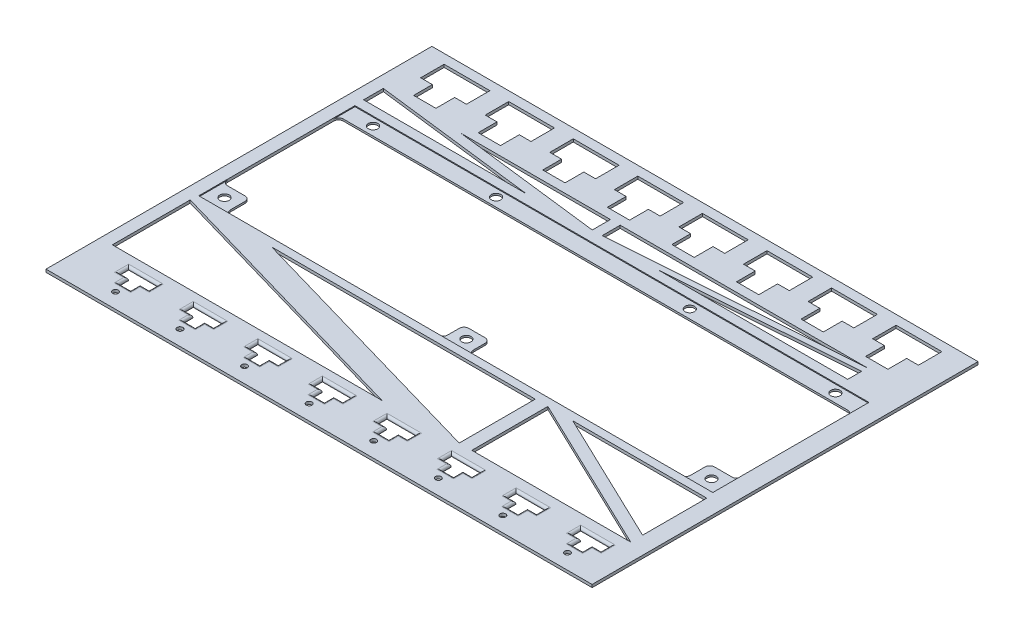
SolidWorks part; units mm, degrees
ref_plane "Front Plane" through (0, 0, 0) normal (0, 0, 1) x (1, 0, 0)
ref_plane "Top Plane" through (0, 0, 0) normal (0, 1, 0) x (1, 0, 0)
ref_plane "Right Plane" through (0, 0, 0) normal (1, 0, 0) x (0, 0, -1)
sketch "Sketch1" plane through (0, 0, 0) normal (0, 1, 0) x (1, 0, 0)
  line L1 (-15, 0) -> (245, 0)
  line L2 (-15, 0) -> (-15, 186.9)
  line L3 (-15, 186.9) -> (245, 186.9)
  line L4 (245, 0) -> (245, 186.9)
  dimension "D1" = 186.9
  dimension "D2" = 260
extrude "Boss-Extrude1" add sketch "Sketch1" along normal blind 1.2
sketch "Sketch2" plane through (0, 0, 0) normal (0, 1, 0) x (1, 0, 0)
  line L0 (245, 186.9) -> (-15, 186.9) construction
  line L1 (17.91, 148.65) -> (236.81, 148.65)
  line L2 (17.91, 148.65) -> (17.91, 82.15)
  line L3 (17.91, 82.15) -> (236.81, 82.15)
  line L4 (236.81, 148.65) -> (236.81, 82.15)
  line L5 (-15, 186.9) -> (-15, 0) construction
  dimension "D1" = 38.25
  dimension "D2" = 32.91
  dimension "D3" = 66.5
  dimension "D4" = 218.9
extrude "Cut-Extrude1" cut sketch "Sketch2" along normal blind 9
sketch "Sketch3" plane through (0, 1.2, 0) normal (0, 1, 0) x (1, 0, 0)
  line L0 (236.81, 148.65) -> (17.91, 148.65) construction
  line L1 (17.91, 148.65) -> (17.91, 82.15) construction
  line L2 (17.91, 82.15) -> (236.81, 82.15) construction
  circle A0 centre (28.91, 145.35) radius 2
  circle A1 centre (81.31, 145.35) radius 2
  circle A2 centre (163.81, 145.35) radius 2
  circle A3 centre (225.81, 145.35) radius 2
  circle A4 centre (23.66, 87.35) radius 2
  circle A5 centre (127.36, 86.65) radius 2
  circle A6 centre (231.06, 87.35) radius 2
  dimension "D3" = 4
  dimension "D4" = 3.3
  dimension "D6" = 3.3
  dimension "D8" = 3.3
  dimension "D10" = 5.2
  dimension "D12" = 4.5
  dimension "D14" = 5.2
  dimension "D1" = 3.3
  dimension "D2" = 11
  dimension "D5" = 52.4
  dimension "D7" = 82.5
  dimension "D9" = 62
  dimension "D11" = 5.75
  dimension "D13" = 103.7
  dimension "D15" = 103.7
sketch "Sketch4" plane through (0, 0, 0) normal (0, 1, 0) x (1, 0, 0)
  line L0 (236.81, 82.15) -> (236.81, 148.65) construction
  line L1 (17.91, 148.65) -> (236.81, 148.65)
  line L2 (17.91, 148.65) -> (17.91, 141.65)
  line L3 (17.91, 141.65) -> (236.81, 141.65)
  line L4 (236.81, 148.65) -> (236.81, 141.65)
  line L5 (17.91, 82.15) -> (236.81, 82.15) construction
  line L6 (236.81, 82.15) -> (225.31, 82.15)
  line L7 (236.81, 82.15) -> (236.81, 92.35)
  line L8 (236.81, 92.35) -> (225.31, 92.35)
  line L9 (225.31, 82.15) -> (225.31, 92.35)
  line L10 (121.86, 82.15) -> (132.86, 82.15)
  line L11 (121.86, 82.15) -> (121.86, 91.15)
  line L12 (121.86, 91.15) -> (132.86, 91.15)
  line L13 (132.86, 82.15) -> (132.86, 91.15)
  line L15 (17.91, 82.15) -> (29.41, 82.15)
  line L16 (17.91, 82.15) -> (17.91, 92.35)
  line L17 (17.91, 92.35) -> (29.41, 92.35)
  line L18 (29.41, 82.15) -> (29.41, 92.35)
  dimension "D1" = 7
  dimension "D2" = 5
  dimension "D3" = 5.75
  dimension "D4" = 4.5
  dimension "D5" = 5.5
  dimension "D6" = 5.5
  dimension "D7" = 5.75
  dimension "D8" = 5
extrude "Boss-Extrude2" add sketch "Sketch4" along normal blind 0.8
extrude "Cut-Extrude2" cut sketch "Sketch3" against normal blind 10
fillet "Fillet1" radius 2 12 edges at (17.91, 0.4, -92.35) (29.41, 0.4, -82.15) (29.41, 0.4, -92.35) (17.91, 0.4, -141.65) (236.81, 0.4, -141.65) (236.81, 0.4, -92.35) (225.31, 0.4, -82.15) (225.31, 0.4, -92.35) (121.86, 0.4, -82.15) (132.86, 0.4, -82.15) (132.86, 0.4, -91.15) (121.86, 0.4, -91.15)
sketch "Sketch10" plane through (0, 1.2, 0) normal (0, 1, 0) x (1, 0, 0)
  line L0 (245, 186.9) -> (-15, 186.9) construction
  line L1 (21.63, 182.9) -> (41.13, 182.9)
  line L2 (21.63, 182.9) -> (21.63, 172.9)
  line L3 (21.63, 172.9) -> (41.13, 172.9)
  line L4 (41.13, 182.9) -> (41.13, 172.9)
  line L5 (17.91, 148.65) -> (17.91, 82.15) construction
  dimension "D1" = 4
  dimension "D2" = 19.5
  dimension "D3" = 3.72
  dimension "D4" = 10
extrude "Cut-Extrude4" cut sketch "Sketch10" against normal up to next (1.2 mm away)
sketch "Sketch11" plane through (0, 1.2, 0) normal (0, 1, 0) x (1, 0, 0)
  line L0 (21.63, 172.9) -> (41.13, 172.9) construction
  line L1 (26.63, 172.9) -> (36.13, 172.9)
  line L2 (26.63, 172.9) -> (26.63, 164.9)
  line L3 (26.63, 164.9) -> (36.13, 164.9)
  line L4 (36.13, 172.9) -> (36.13, 164.9)
  line L5 (41.13, 172.9) -> (41.13, 182.9) construction
  line L6 (21.63, 182.9) -> (21.63, 172.9) construction
  dimension "D1" = 8
  dimension "D2" = 5
  dimension "D3" = 5
extrude "Cut-Extrude5" cut sketch "Sketch11" against normal blind 7
pattern_linear "LPattern1" count 8 spacing 27.5 along (1, 0, 0) of "Cut-Extrude4", "Cut-Extrude5"
sketch "Sketch14" plane through (0, 1.2, 0) normal (0, 1, 0) x (1, 0, 0)
  line L0 (-15, 186.9) -> (-15, 0) construction
  line L1 (29.19, 37) -> (33.04, 37)
  line L2 (29.19, 37) -> (29.19, 41)
  line L3 (29.19, 41) -> (41.89, 41)
  line L4 (41.89, 37) -> (41.89, 41)
  line L5 (38.04, 37) -> (41.89, 37)
  line L7 (-15, 0) -> (245, 0) construction
  line L8 (33.04, 37) -> (33.04, 33)
  line L9 (33.04, 33) -> (38.04, 33)
  line L10 (38.04, 37) -> (38.04, 33)
  circle A0 centre (35.54, 29) radius 1.2
  dimension "D8" = 2.4
  dimension "D9" = 4
  dimension "D10" = 2.5
  dimension "D1" = 44.19
  dimension "D2" = 12.7
  dimension "D3" = 37
  dimension "D4" = 4
  dimension "D5" = 3.85
  dimension "D6" = 3.85
  dimension "D7" = 4
extrude "Cut-Extrude8" cut sketch "Sketch14" against normal up to next (1.2 mm away)
fillet "Fillet2" radius 1 8 edges at (29.19, 1.2, -39) (33.04, 1.2, -35) (31.115, 1.2, -37) (39.965, 1.2, -37) (41.89, 1.2, -39) (35.54, 1.2, -41) (38.04, 1.2, -35) (35.54, 1.2, -33)
pattern_linear "LPattern4" count 8 spacing 27.5 along (1, 0, 0) of "Cut-Extrude8", "Fillet2"
sketch "Sketch15" plane through (0, 1.2, 0) normal (0, 1, 0) x (1, 0, 0)
  line L0 (-15, 0) -> (245, 0) construction
  line L1 (-15, 186.9) -> (12.421, 186.9)
  line L2 (-15, 186.9) -> (-15, 0)
  line L3 (-15, 0) -> (12.421, 0)
  line L4 (12.421, 186.9) -> (12.421, 22.5534)
  line L5 (17.5952, 161.0383) -> (17.5952, 152.6302)
  line L6 (17.5952, 152.6302) -> (86.9298, 152.6302)
  line L7 (86.9298, 152.6302) -> (17.5952, 161.0383)
  line L8 (50.5809, 161.0383) -> (114.3102, 153.3099)
  line L9 (114.3102, 153.3099) -> (114.3102, 161.0383)
  line L10 (114.3102, 161.0383) -> (50.5809, 161.0383)
  line L11 (118.4926, 161.0383) -> (118.4926, 153.3099)
  line L12 (118.4926, 153.3099) -> (223.7881, 161.0383)
  line L13 (223.7881, 161.0383) -> (118.4926, 161.0383)
  line L14 (143.1995, 152.6302) -> (223.7881, 158.5451)
  line L15 (223.7881, 158.5451) -> (223.7881, 152.6302)
  line L16 (223.7881, 152.6302) -> (143.1995, 152.6302)
  line L17 (17.5952, 78.7908) -> (17.5952, 45.6512)
  line L18 (17.5952, 45.6512) -> (132.457, 45.6512)
  line L19 (132.457, 45.6512) -> (17.5952, 78.7908)
  line L20 (52.2625, 78.7908) -> (164.5575, 46.3917)
  line L21 (164.5575, 46.3917) -> (164.5575, 78.7908)
  line L22 (164.5575, 78.7908) -> (52.2625, 78.7908)
  line L23 (169.9222, 78.7908) -> (169.9222, 46.3917)
  line L24 (169.9222, 46.3917) -> (237.5932, 46.3917)
  line L25 (237.5932, 46.3917) -> (169.9222, 78.7908)
  line L26 (180.5213, 78.7908) -> (237.5932, 51.4663)
  line L27 (237.5932, 51.4663) -> (237.5932, 78.7908)
  line L28 (237.5932, 78.7908) -> (180.5213, 78.7908)
  line L30 (12.421, 22.5534) -> (245, 22.5534)
  line L32 (12.421, 0) -> (245, 0)
  line L33 (245, 22.5534) -> (245, 0)
extrude "Cut-Extrude9" cut sketch "Sketch15" against normal blind 10
